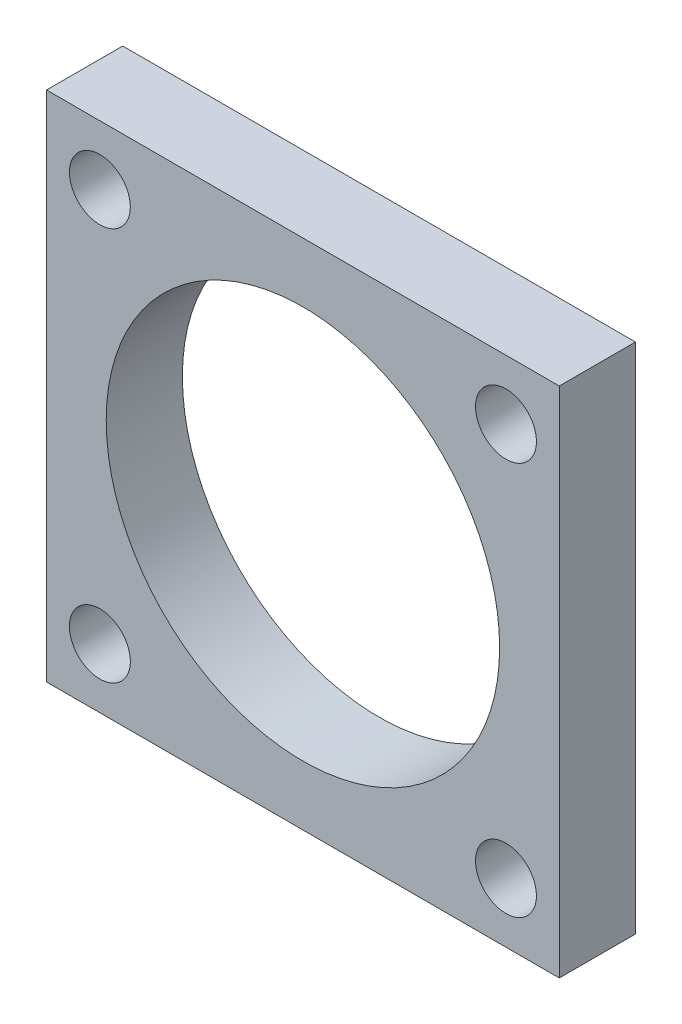
SolidWorks part; units mm, degrees
ref_plane "Front Plane" through (0, 0, 0) normal (0, 0, 1) x (1, 0, 0)
ref_plane "Top Plane" through (0, 0, 0) normal (0, 1, 0) x (1, 0, 0)
ref_plane "Right Plane" through (0, 0, 0) normal (1, 0, 0) x (0, 0, -1)
sketch "Sketch1" plane through (0, 0, 0) normal (0, 0, 1) x (1, 0, 0)
  line L0 (-11.6442, 9.5669) -> (8.5558, 9.5669)
  line L1 (8.5558, 9.5669) -> (8.5558, -10.6331)
  line L2 (8.5558, -10.6331) -> (-11.6442, -10.6331)
  line L3 (-11.6442, -10.6331) -> (-11.6442, 9.5669)
  line L4 (-1.5442, 9.5669) -> (-1.5442, -10.6331) construction
  line L5 (-11.6442, -0.5331) -> (8.5558, -0.5331) construction
  circle A0 centre (-1.5442, -0.5331) radius 7.75
  circle A1 centre (-9.5442, 7.2169) radius 1.2
  circle A2 centre (6.4558, 7.2169) radius 1.2
  circle A3 centre (-9.5442, -8.2831) radius 1.2
  circle A4 centre (6.4558, -8.2831) radius 1.2
  point P12 (-9.6938, 7.4409)
  dimension "D2" = 2.1
  dimension "D1" = 20.2
extrude "Boss-Extrude2" add sketch "Sketch1" along normal blind 3
